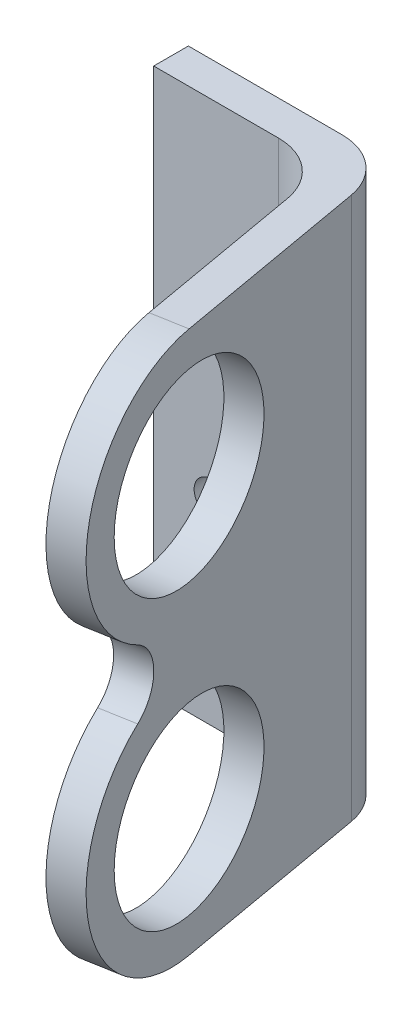
SolidWorks part; units mm, degrees
material "Acrylic (Medium-high impact)"
ref_plane "Front Plane" through (0, 0, 0) normal (0, 0, 1) x (1, 0, 0)
ref_plane "Top Plane" through (0, 0, 0) normal (0, 1, 0) x (1, 0, 0)
ref_plane "Right Plane" through (0, 0, 0) normal (1, 0, 0) x (0, 0, -1)
sketch "Sketch1" plane through (0, 0, 0) normal (0, 1, 0) x (1, 0, 0)
  line L0 (-2.3206, 10.9135) -> (11.0012, 10.9135)
  line L1 (15.9252, 6.7817) -> (20.8433, -21.1098)
  line L2 (20.8433, -21.1098) -> (17.8888, -21.6308)
  line L3 (17.8888, -21.6308) -> (13.4079, 3.7817)
  line L4 (8.4839, 7.9135) -> (-2.3206, 7.9135)
  line L5 (-2.3206, 7.9135) -> (-2.3206, 10.9135)
  arc A0 (15.9252, 6.7817) -> (11.0012, 10.9135) centre (11.0012, 5.9135) ccw
  arc A1 (13.4079, 3.7817) -> (8.4839, 7.9135) centre (8.4839, 2.9135) ccw
  point P2 (43.8493, -40.5738)
  dimension "D5" = 5
  dimension "D1" = 3
  dimension "D2" = 100
extrude "Boss-Extrude1" add sketch "Sketch1" along normal blind 47
sketch "Sketch2" plane through (0, 0, -7.9135) normal (0, 0, 1) x (1, 0, 0)
  line L0 (-2.3206, 47) -> (-2.3206, 0) construction
  line L1 (2.6794, 30) -> (2.6794, 47) construction
  line L2 (-2.3206, 47) -> (8.4839, 47) construction
  line L3 (2.6794, 17) -> (2.6794, 0) construction
  line L4 (-2.3206, 0) -> (8.4839, 0) construction
  circle A0 centre (2.6794, 30) radius 1.5
  circle A1 centre (2.6794, 17) radius 1.5
  dimension "D2" = 3
  dimension "D1" = 5
  dimension "D3" = 13
extrude "Cut-Extrude1" cut sketch "Sketch2" against normal through all
sketch "Sketch3" plane through (13.6504, 0, -2.4069) normal (-0.9848, 0, 0.1736) x (0.1736, 0, 0.9848)
  line L0 (13.4085, 11) -> (13.4085, 0) construction
  line L1 (-1.396, 0) -> (24.4085, 0) construction
  line L2 (13.4085, 36) -> (13.4085, 47) construction
  line L3 (-1.396, 47) -> (24.4085, 47) construction
  line L4 (24.4085, 47) -> (24.4085, 0) construction
  line L5 (13.4085, 47) -> (24.4085, 47)
  line L6 (24.4085, 47) -> (24.4085, 36)
  line L7 (13.4085, 0) -> (24.4085, 0)
  line L8 (24.4085, 0) -> (24.4085, 11)
  circle A0 centre (13.4085, 36) radius 8
  circle A1 centre (13.4085, 11) radius 8
  circle A2 centre (13.4085, 36) radius 11
  circle A3 centre (13.4085, 11) radius 11
  arc A4 (18.8949, 20.5342) -> (18.8949, 26.4658) centre (20.6015, 23.5) cw
  line M3 (-1.396, 0) -> (24.4085, 0)
  line M4 (24.4085, 0) -> (24.4085, 47)
  line M5 (24.4085, 47) -> (-1.396, 47)
  dimension "D1" = 16
  dimension "D2" = 22
  dimension "D3" = 25
extrude "Cut-Extrude2" cut sketch "Sketch3" against normal through all contours A2 M4 M5 | A3 M3 M4 | A1 | A0 | A4 A3 A2 M4
